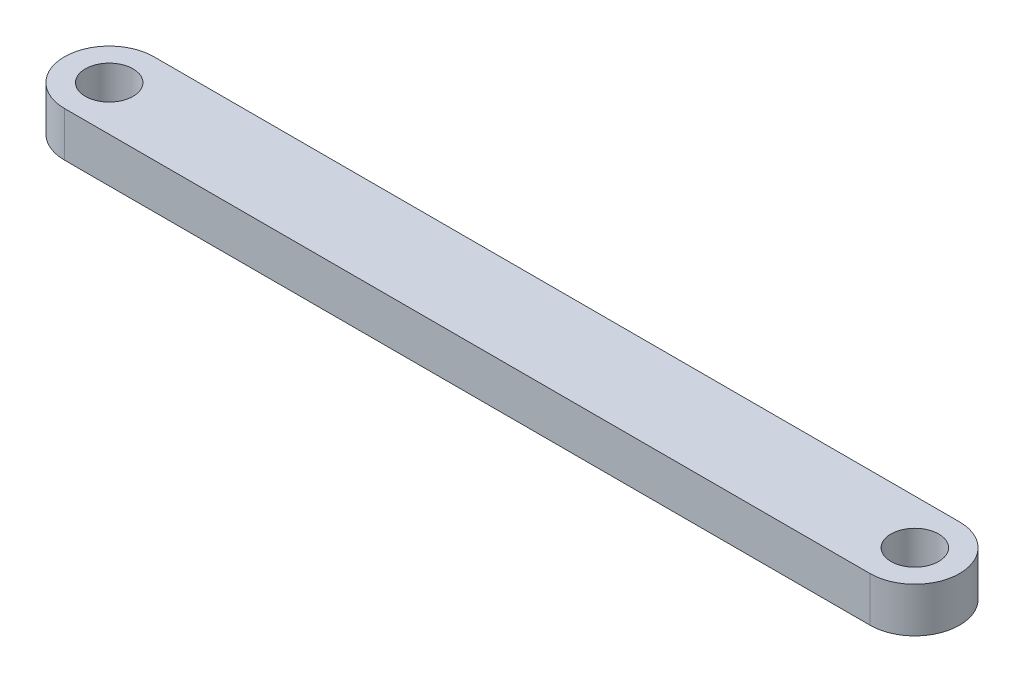
SolidWorks part; units mm, degrees
ref_plane "前视基准面" through (0, 0, 0) normal (0, 0, 1) x (1, 0, 0)
ref_plane "上视基准面" through (0, 0, 0) normal (0, 1, 0) x (1, 0, 0)
ref_plane "右视基准面" through (0, 0, 0) normal (1, 0, 0) x (0, 0, -1)
sketch "草图1" plane through (0, 0, 0) normal (0, 1, 0) x (1, 0, 0)
  line L0 (-54, -3) -> (0, -3)
  line L1 (-54, 3) -> (0, 3)
  arc A0 (0, -3) -> (0, 3) centre (0, 0) ccw
  arc A1 (-54, 3) -> (-54, -3) centre (-54, 0) ccw
  dimension "D2" = 3
  dimension "D3" = 3
  dimension "D1" = 54
extrude "凸台-拉伸1" add sketch "草图1" along normal blind 3
sketch "草图2" plane through (0, 3, 0) normal (0, 1, 0) x (1, 0, 0)
  circle A0 centre (-54, 0) radius 1.6
  circle A1 centre (0, 0) radius 1.6
  dimension "D1" = 3.2
  dimension "D2" = 3.2
extrude "切除-拉伸1" cut sketch "草图2" against normal through all
